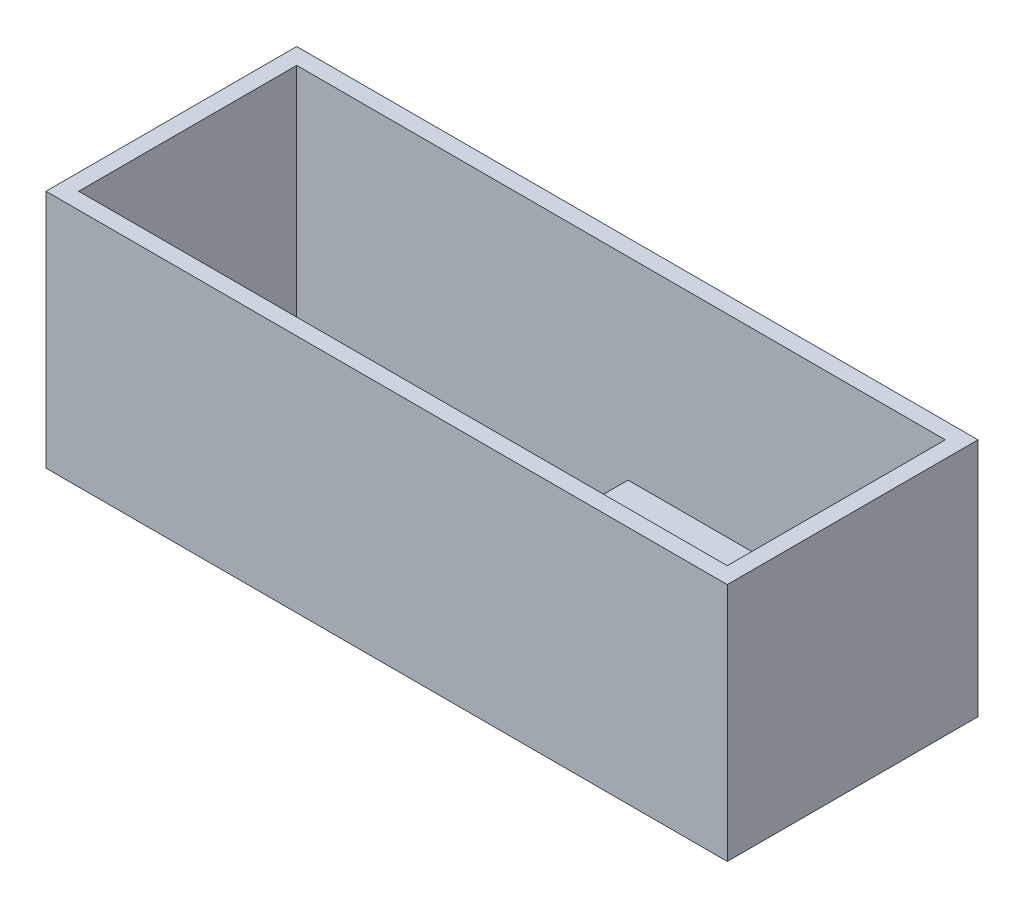
SolidWorks part; units mm, degrees
ref_plane "Front Plane" through (0, 0, 0) normal (0, 0, 1) x (1, 0, 0)
ref_plane "Top Plane" through (0, 0, 0) normal (0, 1, 0) x (1, 0, 0)
ref_plane "Right Plane" through (0, 0, 0) normal (1, 0, 0) x (0, 0, -1)
sketch "Sketch1" plane through (0, 0, 0) normal (0, 1, 0) x (1, 0, 0)
  line L1 (-59.5, -20) -> (59.5, -20)
  line L2 (-59.5, -20) -> (-59.5, 20)
  line L3 (-59.5, 20) -> (59.5, 20)
  line L4 (59.5, -20) -> (59.5, 20)
  line L5 (-59.5, -20) -> (59.5, 20) construction
  line L6 (-59.5, 20) -> (59.5, -20) construction
  point P0 (0, 0)
  dimension "D1" = 119
  dimension "D2" = 40
extrude "Boss-Extrude1" add sketch "Sketch1" along normal blind 4
sketch "Sketch2" plane through (0, 0, 0) normal (0, 1, 0) x (1, 0, 0)
  line L1 (59.5, -20) -> (-59.5, -20)
  line L2 (59.5, -20) -> (59.5, 20)
  line L3 (59.5, 20) -> (-59.5, 20)
  line L4 (-59.5, -20) -> (-59.5, 20)
  line L5 (59.5, -20) -> (-59.5, 20) construction
  line L6 (59.5, 20) -> (-59.5, -20) construction
  line L7 (-62.5, -23) -> (62.5, -23)
  line L8 (-62.5, -23) -> (-62.5, 23)
  line L9 (-62.5, 23) -> (62.5, 23)
  line L10 (62.5, -23) -> (62.5, 23)
  line L11 (-62.5, -23) -> (62.5, 23) construction
  line L12 (-62.5, 23) -> (62.5, -23) construction
  point P0 (0, 0)
  point P7 (0, 0)
  dimension "D1" = 3
  dimension "D2" = 3
extrude "Boss-Extrude2" add sketch "Sketch2" along normal blind 44
sketch "Sketch3" plane through (0, 4, 0) normal (0, 1, 0) x (1, 0, 0)
  line L0 (-59.5, -20) -> (59.5, -20) construction
  line L1 (1.3, -20) -> (59.5, -20)
  line L2 (1.3, -20) -> (1.3, 20)
  line L3 (1.3, 20) -> (59.5, 20)
  line L4 (59.5, -20) -> (59.5, 20)
  dimension "D1" = 58.2
extrude "Boss-Extrude3" add sketch "Sketch3" along normal blind 3
sketch "Sketch4" plane through (0, 7, 0) normal (0, 1, 0) x (1, 0, 0)
  line L0 (1.3, -20) -> (59.5, -20) construction
  line L1 (1.3, 20) -> (29.3, 20)
  line L2 (1.3, 20) -> (1.3, -20)
  line L3 (1.3, -20) -> (29.3, -20)
  line L4 (29.3, 20) -> (29.3, -20)
  dimension "D1" = 28
extrude "Boss-Extrude4" add sketch "Sketch4" along normal blind 1.5
